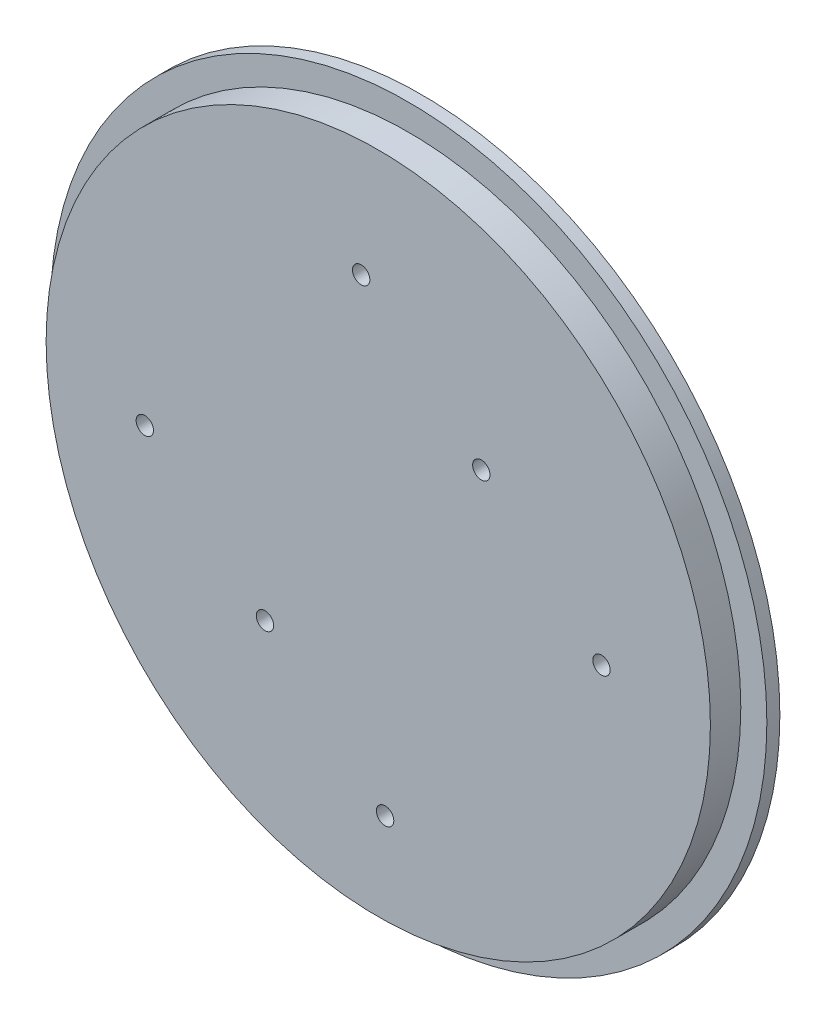
SolidWorks part; units mm, degrees
ref_plane "Plano frontal" through (0, 0, 0) normal (0, 0, 1) x (1, 0, 0)
ref_plane "Plano superior" through (0, 0, 0) normal (0, 1, 0) x (1, 0, 0)
ref_plane "Plano direito" through (0, 0, 0) normal (1, 0, 0) x (0, 0, -1)
sketch "Esboço1" plane through (0, 0, 0) normal (0, 0, 1) x (1, 0, 0)
  circle A0 centre (0, 0) radius 14 construction
  circle A1 centre (0, 0) radius 14
  circle A2 centre (0, 0) radius 82.5
  dimension "D1" = 165
extrude "Ressalto-extrusão1" add sketch "Esboço1" along normal blind 3
sketch "Esboço2" plane through (0, 0, 0) normal (0, 0, -1) x (-1, 0, 0)
  line L0 (0, 0) -> (15.1208, -54.9578)
  line L1 (0, 0) -> (40.0345, 40.5739)
  circle A1 centre (0, 0) radius 57 construction
  circle A2 centre (15.1208, -54.9578) radius 14 construction
  circle A3 centre (-55.1553, 14.3839) radius 14 construction
  circle A4 centre (40.0345, 40.5739) radius 14 construction
  circle A5 centre (-55.1553, 14.3839) radius 5.925
  circle A6 centre (40.0345, 40.5739) radius 5.925
  circle A7 centre (15.1208, -54.9578) radius 5.925
  point P14 (0, 0)
  dimension "D1" = 57
  dimension "D3" = 3
  dimension "D4" = 11.85
  dimension "D2" = 57
extrude "Ressalto-extrusão2" add sketch "Esboço2" along normal blind 8
sketch "Esboço3" plane through (0, 0, 3) normal (0, 0, 1) x (1, 0, 0)
  circle A0 centre (0, 0) radius 14
extrude "Ressalto-extrusão3" add sketch "Esboço3" against normal blind 3
sketch "Esboço4" plane through (0, 0, 3) normal (0, 0, 1) x (1, 0, 0)
  circle A0 centre (0, 0) radius 10
  circle A1 centre (0, 0) radius 14
  circle A2 centre (0, 0) radius 14 construction
  dimension "D1" = 0
extrude "Ressalto-extrusão4" add sketch "Esboço4" against normal up to surface (11 mm away) up to face at (49.2303, 14.3839, -8)
sketch "Esboço5" plane through (0, 0, -8) normal (0, 0, -1) x (-1, 0, 0)
  circle A0 centre (0, 0) radius 3.05
extrude "Corte-extrusão1" cut sketch "Esboço5" against normal blind 1
sketch "Esboço6" plane through (0, 0, 3) normal (0, 0, 1) x (1, 0, 0)
  circle A0 centre (0, 0) radius 77.5 construction
  circle A1 centre (0, 0) radius 76.5
  dimension "D1" = 1
extrude "Ressalto-extrusão5" add sketch "Esboço6" along normal blind 7
sketch "Esboço13" plane through (0, 0, 0) normal (0, 0, -1) x (-1, 0, 0)
  circle A0 centre (-1.5735, -55.5495) radius 2
  circle A1 centre (26.098, -30.4634) radius 2
  circle A2 centre (53.7695, -5.3774) radius 2
  circle A3 centre (-51.4072, -0.5797) radius 2
  circle A4 centre (-23.7357, 24.5064) radius 2
  circle A5 centre (3.9358, 49.5924) radius 2
  point P2 (-1.5735, -57.0495)
  point P3 (1.7669, -53.5235)
  point P4 (-1.5735, -55.5495)
  point P5 (0, 0)
  point P8 (26.098, -30.4634)
  point P11 (53.7695, -5.3774)
  point P14 (-126.6244, -16.8708)
  point P17 (-120.9992, 2.7206)
  point P20 (-5.7787, 54.7055)
  point P21 (-25.1761, 28.1311)
  point P22 (-48.453, -11.6335)
  point P23 (-51.4072, -0.5797)
  point P24 (-23.7357, 24.5064)
  point P25 (3.9358, 49.5924)
  point P26 (0, 0)
  point P27 (0, 0)
  point P28 (0, 0)
  point P30 (-19.5198, 26.1476)
  dimension "D1" = 37.35
  dimension "D2" = 37.35
  dimension "D3" = 37.35
  dimension "D4" = 37.35
  dimension "D5" = 74.1962
  dimension "D8" = 40.1139
  dimension "D9" = 34.1167
extrude "Corte-extrusão2" cut sketch "Esboço13" against normal through all
sketch "Esboço14" plane through (0, 0, 0) normal (0, 0, -1) x (-1, 0, 0)
  circle A0 centre (53.7695, -5.3774) radius 2 construction
  circle A1 centre (26.098, -30.4634) radius 2 construction
  circle A2 centre (-1.5735, -55.5495) radius 2 construction
  circle A3 centre (3.9358, 49.5924) radius 2 construction
  circle A4 centre (-23.7357, 24.5064) radius 2 construction
  circle A5 centre (-51.4072, -0.5797) radius 2 construction
  circle A6 centre (53.7695, -5.3774) radius 2
  circle A7 centre (26.098, -30.4634) radius 2
  circle A8 centre (-1.5735, -55.5495) radius 2
  circle A9 centre (3.9358, 49.5924) radius 2
  circle A10 centre (-23.7357, 24.5064) radius 2
  circle A11 centre (-51.4072, -0.5797) radius 2
  circle A12 centre (53.7695, -5.3774) radius 7.5
  circle A13 centre (26.098, -30.4634) radius 7.5
  circle A14 centre (-1.5735, -55.5495) radius 7.5
  circle A15 centre (3.9358, 49.5924) radius 7.5
  circle A16 centre (-23.7357, 24.5064) radius 7.5
  circle A17 centre (-51.4072, -0.5797) radius 7.5
  dimension "D1" = 5.5
extrude "Corte-extrusão3" cut sketch "Esboço14" against normal blind 5 contours A17 | A16 | A15 | A12 | A13 | A14
